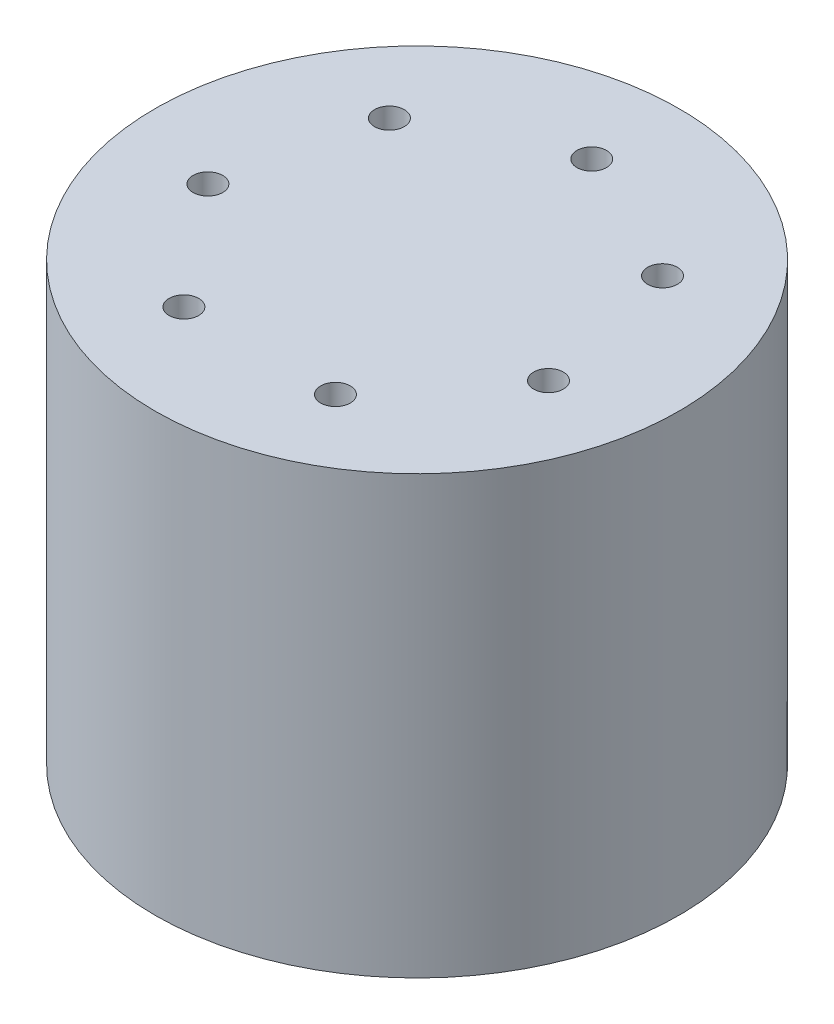
SolidWorks part; units mm, degrees
ref_plane "前基準面" through (0, 0, 0) normal (0, 0, 1) x (1, 0, 0)
ref_plane "上基準面" through (0, 0, 0) normal (0, 1, 0) x (1, 0, 0)
ref_plane "右基準面" through (0, 0, 0) normal (1, 0, 0) x (0, 0, -1)
sketch "草圖1" plane through (0, 0, 0) normal (0, 1, 0) x (1, 0, 0)
  circle A0 centre (0, 0) radius 60
  dimension "D2" = 120
extrude "填料-伸長1" add sketch "草圖1" along normal blind 100
sketch "草圖2" plane through (0, 100, 0) normal (0, 1, 0) x (1, 0, 0)
  circle A0 centre (0, 0) radius 40 construction
  circle A1 centre (0, 40) radius 4
  circle A2 centre (31.2733, 24.9396) radius 4
  circle A3 centre (38.9971, -8.9008) radius 4
  circle A4 centre (17.3553, -36.0388) radius 4
  circle A5 centre (-17.3553, -36.0388) radius 4
  circle A6 centre (-38.9971, -8.9008) radius 4
  circle A7 centre (-31.2733, 24.9396) radius 4
  point P6 (32.2491, 23.3152)
  point P7 (0, 0)
  point P19 (0, 0)
  dimension "D1" = 8
  dimension "D2" = 80
  dimension "D3" = 7
hole_wizard "M8 螺紋孔1" positions "3D草圖1" profile "草圖3" tap size "M8" standard "ISO"
sketch3d "3D草圖1"
  point P0 (0, 100, -40)
  point P3 (31.2733, 100, -24.9396)
  point P6 (38.9971, 100, 8.9008)
  point P9 (17.3553, 100, 36.0388)
  point P12 (-17.3553, 100, 36.0388)
  point P15 (-38.9971, 100, 8.9008)
  point P18 (-31.2733, 100, -24.9396)
sketch "草圖3" plane through (0, 100, -40) normal (1, 0, 0) x (0, 0, 1)
  line L0 (0, 0) -> (0, 24.2929)
  line L1 (0, 24.2929) -> (3.4, 22.25)
  line L2 (3.4, 22.25) -> (3.4, 0)
  line L5 (3.4, 0) -> (0, 0)
  line L10 (0, 24.2929) -> (-3.4, 22.25) construction
  line L11 (0, -6.35) -> (0, 107.95) construction
  dimension "螺孔鑽直徑" = 6.8
  dimension "螺孔鑽深度" = 22.25
  dimension "導頭角度" = 118
cosmetic thread "鑽孔螺紋1"
cosmetic thread "鑽孔螺紋2"
cosmetic thread "鑽孔螺紋3"
cosmetic thread "鑽孔螺紋4"
cosmetic thread "鑽孔螺紋5"
cosmetic thread "鑽孔螺紋6"
cosmetic thread "鑽孔螺紋7"
